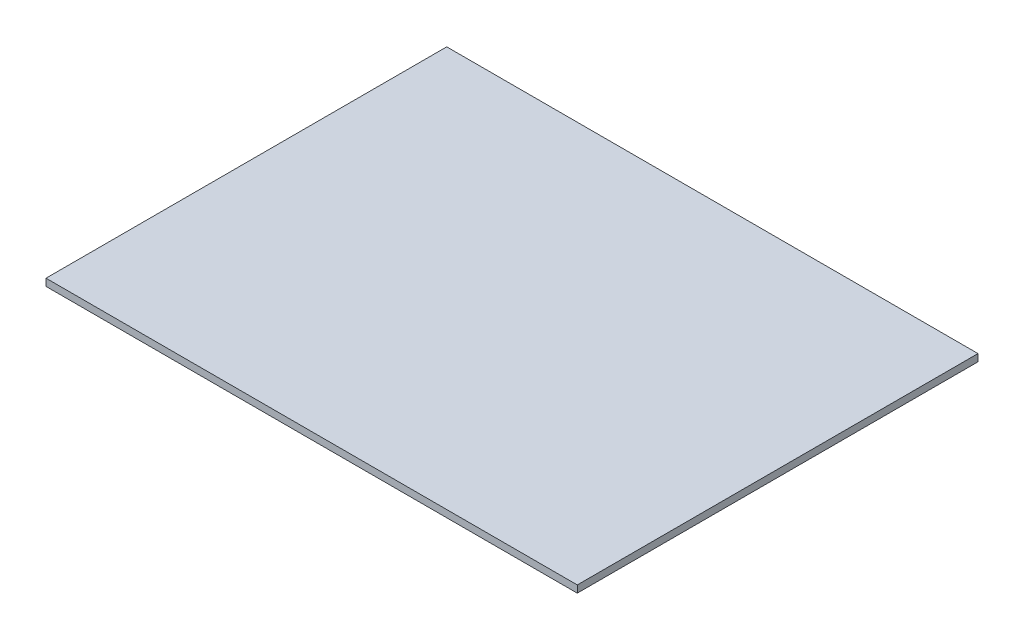
SolidWorks part; units mm, degrees
ref_plane "Front Plane" through (0, 0, 0) normal (0, 0, 1) x (1, 0, 0)
ref_plane "Top Plane" through (0, 0, 0) normal (0, 1, 0) x (1, 0, 0)
ref_plane "Right Plane" through (0, 0, 0) normal (1, 0, 0) x (0, 0, -1)
sketch "Sketch1" plane through (0, 0, 0) normal (0, 1, 0) x (1, 0, 0)
  line L1 (0, 0) -> (446, 0)
  line L2 (0, 0) -> (0, 336.4)
  line L3 (0, 336.4) -> (446, 336.4)
  line L4 (446, 0) -> (446, 336.4)
  dimension "D1" = 446
  dimension "D2" = 336.4
extrude "Boss-Extrude1" add sketch "Sketch1" along normal blind 6
